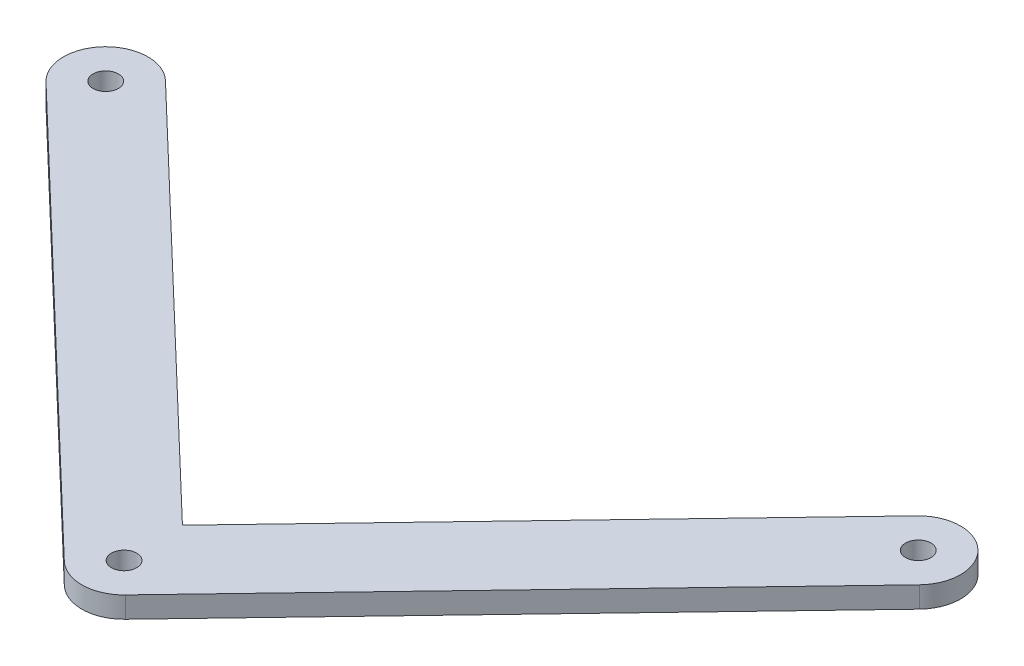
SolidWorks part; units mm, degrees
ref_plane "Front Plane" through (0, 0, 0) normal (0, 0, 1) x (1, 0, 0)
ref_plane "Top Plane" through (0, 0, 0) normal (0, 1, 0) x (1, 0, 0)
ref_plane "Right Plane" through (0, 0, 0) normal (1, 0, 0) x (0, 0, -1)
sketch "Sketch1" plane through (0, 0, 0) normal (0, 1, 0) x (1, 0, 0)
  line L4 (-107.345, 88.871) -> (0.3119, -14.1387) construction
  line L9 (0, 0) -> (91.9484, 96.0963) construction
  line L10 (91.9484, 96.0963) -> (-100.4316, 96.0963) construction
  line L11 (-100.4316, 96.0963) -> (0, 0) construction
  line L12 (-107.345, 88.871) -> (-6.9134, -7.2253)
  line L13 (7.2253, -6.9134) -> (99.1737, 89.1829)
  line L14 (-93.5182, 103.3216) -> (-0.3119, 14.1387)
  line L15 (-0.3119, 14.1387) -> (84.7231, 103.0097)
  line L16 (0.3119, -14.1387) -> (99.1737, 89.1829) construction
  arc A11 (-93.5182, 103.3216) -> (-107.345, 88.871) centre (-100.4316, 96.0963) ccw
  arc A12 (99.1737, 89.1829) -> (84.7231, 103.0097) centre (91.9484, 96.0963) ccw
  arc A13 (-6.9134, -7.2253) -> (7.2253, -6.9134) centre (0, 0) ccw
  circle A14 centre (-100.4316, 96.0963) radius 3
  circle A15 centre (91.9484, 96.0963) radius 3
  circle A16 centre (0, 0) radius 3
  dimension "D1" = 192.38
  dimension "D3" = 139
  dimension "D4" = 20
  dimension "D5" = 6
  dimension "D7" = 6
  dimension "D2" = 133
  dimension "D6" = 6
extrude "Boss-Extrude2" add sketch "Sketch1" along normal blind 5
